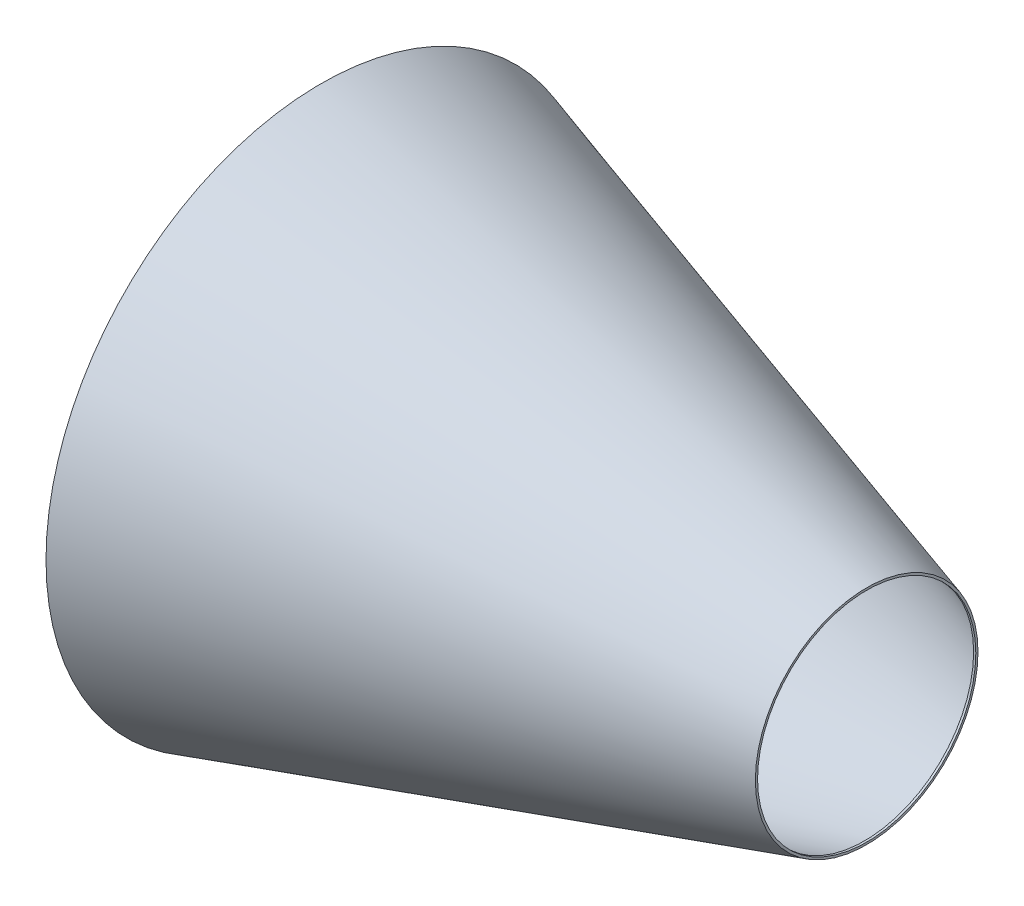
SolidWorks part; units mm, degrees
material "Gray Cast Iron"
ref_plane "Front Plane" through (0, 0, 0) normal (0, 0, 1) x (1, 0, 0)
ref_plane "Top Plane" through (0, 0, 0) normal (0, 1, 0) x (1, 0, 0)
ref_plane "Right Plane" through (0, 0, 0) normal (1, 0, 0) x (0, 0, -1)
sketch "Sketch2" plane through (0, 0, 0) normal (0, 0, 1) x (1, 0, 0)
  line L0 (0, 0) -> (0, -252)
  line L1 (0, 0) -> (500, 0)
  line L2 (500, 0) -> (500, -102)
  line L3 (0, -252) -> (500, -102)
  line L4 (2, -249.3119) -> (498, -100.5119)
  line L5 (498, -2) -> (498, -100.5119)
  line L6 (2, -2) -> (498, -2)
  line L7 (2, -2) -> (2, -249.3119)
  dimension "D1" = 2
revolve "Revolve2" add sketch "Sketch2" angle 360 about L1
sketch "Sketch3" plane through (0, 0, 0) normal (-1, 0, 0) x (0, 0, 1)
  circle A2 centre (0, 0) radius 250
extrude "Cut-Extrude7" cut sketch "Sketch3" against normal blind 2
sketch "Sketch6" plane through (2, 0, 0) normal (-1, 0, 0) x (0, 0, 1)
  circle A0 centre (0, 0) radius 2
extrude "Cut-Extrude8" cut sketch "Sketch6" against normal blind 498
sketch "Sketch7" plane through (500, 0, 0) normal (1, 0, 0) x (0, 0, -1)
  circle A0 centre (0, 0) radius 100
extrude "Cut-Extrude9" cut sketch "Sketch7" against normal blind 2
